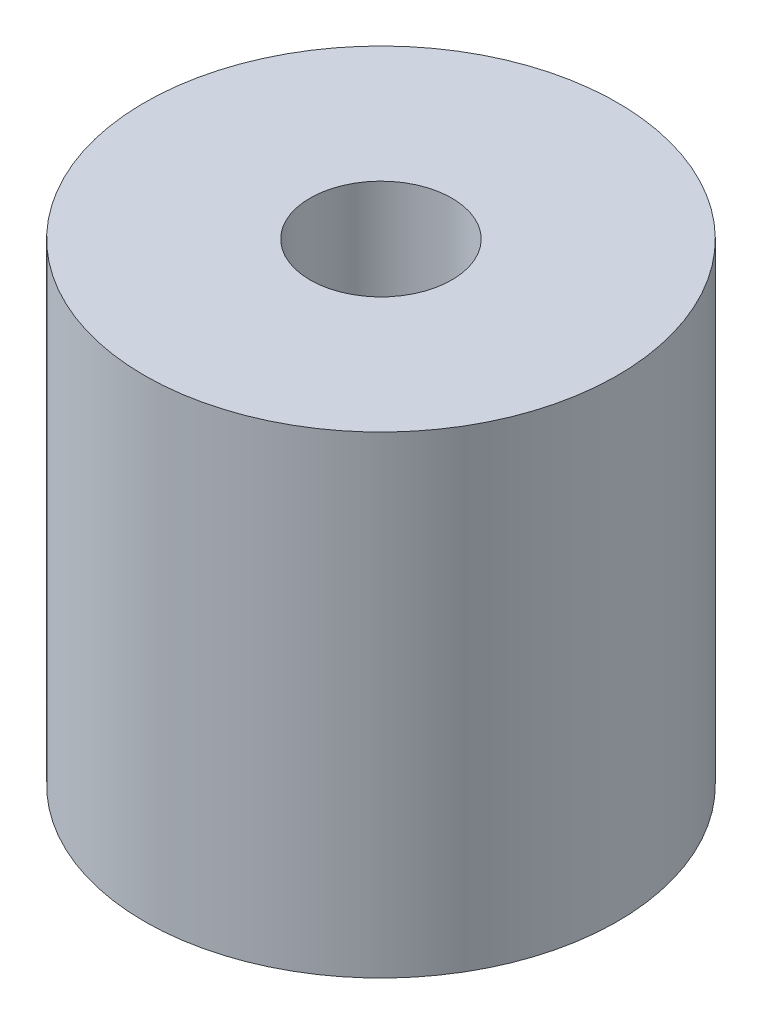
SolidWorks part; units mm, degrees
ref_plane "Front Plane" through (0, 0, 0) normal (0, 0, 1) x (1, 0, 0)
ref_plane "Top Plane" through (0, 0, 0) normal (0, 1, 0) x (1, 0, 0)
ref_plane "Right Plane" through (0, 0, 0) normal (1, 0, 0) x (0, 0, -1)
sketch "Sketch1" plane through (0, 0, 0) normal (0, 1, 0) x (1, 0, 0)
  circle A0 centre (0, 0) radius 5
  circle A1 centre (0, 0) radius 1.5
  dimension "D1" = 10
  dimension "D2" = 3
extrude "Boss-Extrude1" add sketch "Sketch1" along normal blind 10
equation "\"OD\"=10"
equation "\"D1@Sketch1\"=\"OD\""
equation "\"SCREW\"=3"
equation "\"D2@Sketch1\"=\"SCREW\""
equation "\"H\"=10"
equation "\"D1@Boss-Extrude1\"=\"H\""
